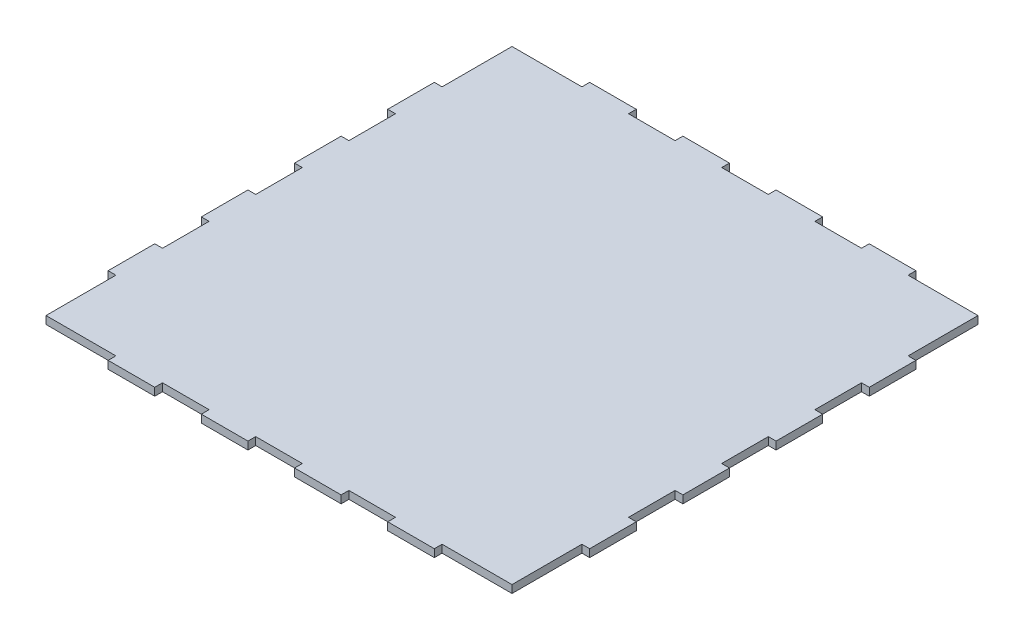
SolidWorks part; units mm, degrees
ref_plane "Plan de face" through (0, 0, 0) normal (0, 0, 1) x (1, 0, 0)
ref_plane "Plan de dessus" through (0, 0, 0) normal (0, 1, 0) x (1, 0, 0)
ref_plane "Plan de droite" through (0, 0, 0) normal (1, 0, 0) x (0, 0, -1)
sketch "Esquisse1" plane through (0, 0, 0) normal (0, 1, 0) x (1, 0, 0)
  line L4 (-190.5, -190.5) -> (190.5, -190.5)
  line L5 (190.5, 190.5) -> (190.5, -190.5)
  line L44 (-190.5, -190.5) -> (-190.5, 190.5)
  line L45 (-190.5, 190.5) -> (190.5, 190.5)
  point P0 (0, 190.5)
  point P6 (190.5, 0)
  dimension "D1" = 381
  dimension "D2" = 381
extrude "Boss.-Extru.1" add sketch "Esquisse1" along normal blind 6.35
sketch "Esquisse2" plane through (190.5, 0, 0) normal (1, 0, 0) x (0, 0, -1)
  line L0 (-190.5, 6.35) -> (190.5, 6.35) construction
  line L1 (-133.35, 6.35) -> (-95.25, 6.35)
  line L2 (-133.35, 6.35) -> (-133.35, 0)
  line L3 (-133.35, 0) -> (-95.25, 0)
  line L4 (-95.25, 6.35) -> (-95.25, 0)
  line L5 (-190.5, 0) -> (190.5, 0) construction
  line L6 (-190.5, 6.35) -> (-190.5, 0) construction
  dimension "D1" = 38.1
  dimension "D2" = 57.15
extrude "Boss.-Extru.2" add sketch "Esquisse2" along normal blind 6.35
pattern_linear "Répétition linéaire1" count 4 spacing 76.2 along (0, 0, -1) of "Boss.-Extru.2"
mirror "Symétrie1" about plane through (0, 0, 0) normal (1, 0, 0) of "Répétition linéaire1", "Boss.-Extru.2"
sketch "Esquisse3" plane through (0, 0, 190.5) normal (0, 0, 1) x (1, 0, 0)
  line L0 (-190.5, 6.35) -> (190.5, 6.35) construction
  line L1 (133.35, 6.35) -> (95.25, 6.35)
  line L2 (133.35, 6.35) -> (133.35, 0)
  line L3 (133.35, 0) -> (95.25, 0)
  line L4 (95.25, 6.35) -> (95.25, 0)
  line L5 (-190.5, 0) -> (190.5, 0) construction
  line L6 (190.5, 6.35) -> (190.5, 0) construction
  dimension "D1" = 38.1
  dimension "D2" = 57.15
extrude "Boss.-Extru.3" add sketch "Esquisse3" along normal blind 6.35
pattern_linear "Répétition linéaire2" count 4 spacing 76.2 along (-1, 0, 0) of "Boss.-Extru.3"
mirror "Symétrie2" about plane through (0, 0, 0) normal (0, 0, 1) of "Répétition linéaire2", "Boss.-Extru.3"
